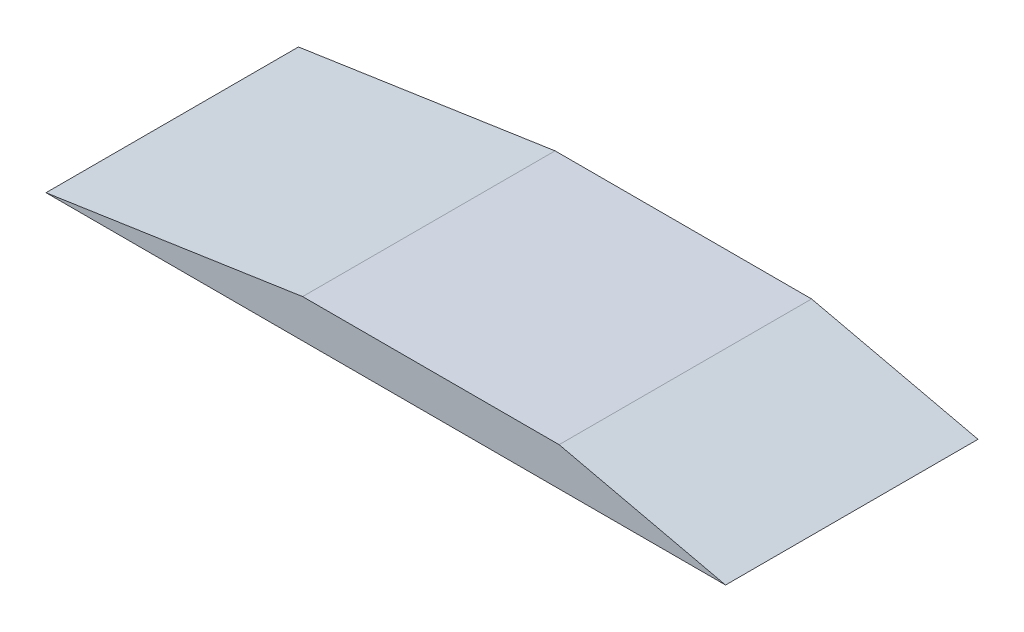
SolidWorks part; units mm, degrees
ref_plane "前视基准面" through (0, 0, 0) normal (0, 0, 1) x (1, 0, 0)
ref_plane "上视基准面" through (0, 0, 0) normal (0, 1, 0) x (1, 0, 0)
ref_plane "右视基准面" through (0, 0, 0) normal (1, 0, 0) x (0, 0, -1)
other "Configuration Table"
sketch "草图2" plane through (0, 0, 0) normal (0, 0, 1) x (1, 0, 0)
  line L0 (-95.0002, -47.2484) -> (921.3131, -47.2484)
  line L1 (-95.0002, -47.2484) -> (413.2956, 28.7008)
  line L2 (413.2956, 28.7008) -> (921.3131, 28.7008)
  line L3 (921.3131, 28.7008) -> (1250.9593, -47.2484)
  line L4 (1250.9593, -47.2484) -> (921.3131, -47.2484)
  dimension "D1" = 1016.3133
extrude "凸台-拉伸1" add sketch "草图2" along normal blind 500 contours L0 L4 L3 L2 L1
